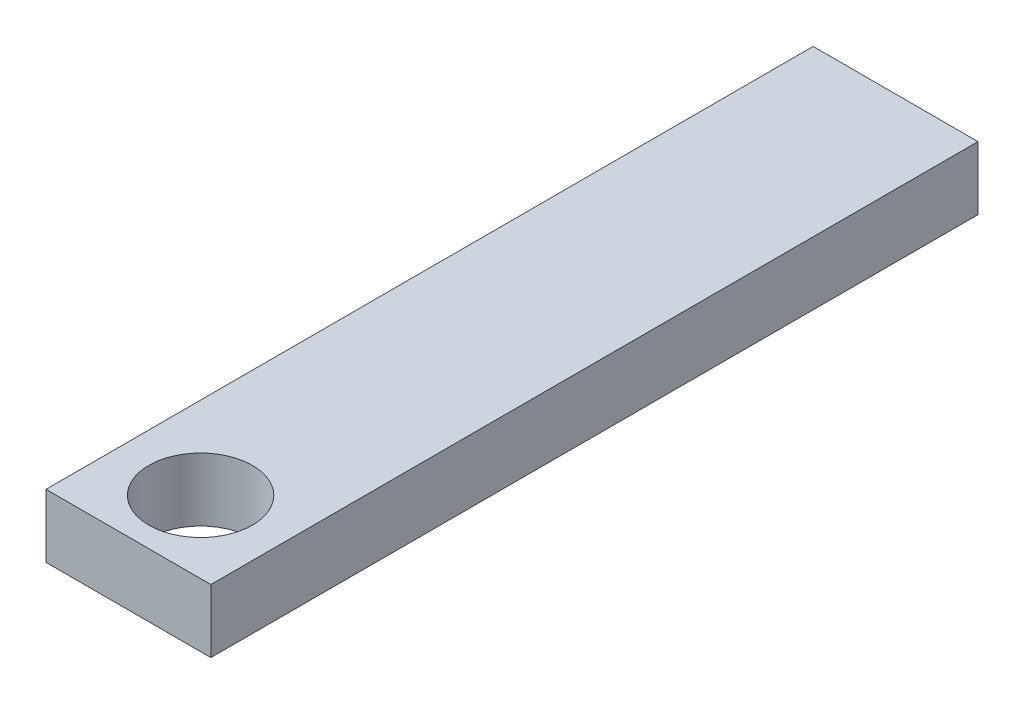
SolidWorks part; units mm, degrees
ref_plane "Front Plane" through (0, 0, 0) normal (0, 0, 1) x (1, 0, 0)
ref_plane "Top Plane" through (0, 0, 0) normal (0, 1, 0) x (1, 0, 0)
ref_plane "Right Plane" through (0, 0, 0) normal (1, 0, 0) x (0, 0, -1)
sketch "Sketch1" plane through (0, 0, 0) normal (0, 1, 0) x (1, 0, 0)
  line L0 (0, 0) -> (6.618, 0)
  line L1 (6.618, 0) -> (6.618, -25.4507)
  line L3 (0, -25.4507) -> (0, 0)
  line L6 (0, -25.4507) -> (0, -27.9)
  line L7 (0, -27.9) -> (0, -30.797)
  line L8 (0, -30.797) -> (6.618, -30.797)
  line L9 (6.618, -30.797) -> (6.618, -25.4507)
  circle A0 centre (3.309, -27.9) radius 2.079
  dimension "D5" = 4.158
  dimension "D1" = 6.618
extrude "Boss-Extrude1" add sketch "Sketch1" along normal blind 2.54
